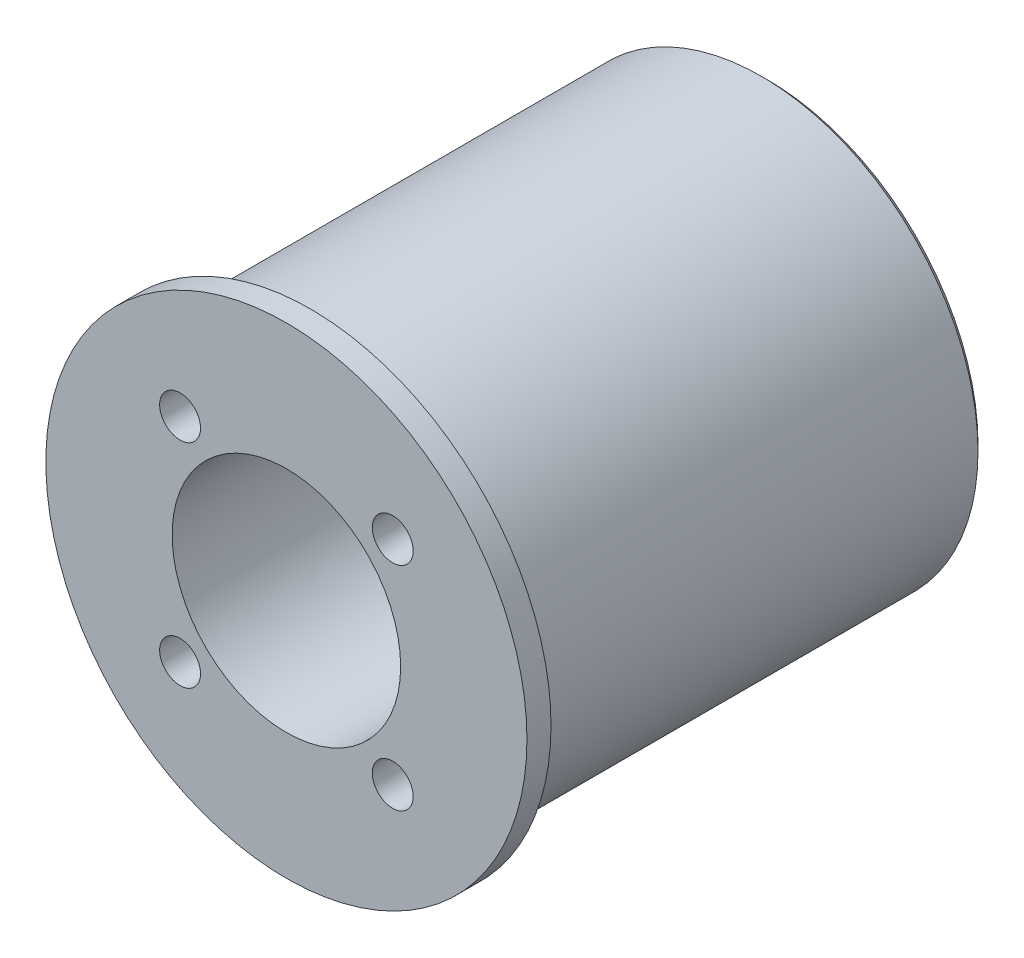
SolidWorks part; units mm, degrees
material "AISI 1020 Acier laminé à froid"
ref_plane "Plan de face" through (0, 0, 0) normal (0, 0, 1) x (1, 0, 0)
ref_plane "Plan de dessus" through (0, 0, 0) normal (0, 1, 0) x (1, 0, 0)
ref_plane "Plan de droite" through (0, 0, 0) normal (1, 0, 0) x (0, 0, -1)
sketch "Esquisse1" plane through (0, 0, 0) normal (0, 0, 1) x (1, 0, 0)
  circle A0 centre (0, 0) radius 18
  dimension "D1" = 36
extrude "Boss.-Extru.1" add sketch "Esquisse1" along normal blind 40
sketch "Sketch1" plane through (0, 0, 40) normal (0, 0, 1) x (1, 0, 0)
  circle A0 centre (0, 0) radius 20
  dimension "D1" = 40
extrude "Boss-Extrude1" add sketch "Sketch1" against normal blind 2
hole_wizard "CBORE for M3 Hex Socket Head Cap Screw1" positions "Esquisse2" profile "Esquisse4" counterbore size "M3" standard "ISO" end condition through all
sketch "Esquisse2" plane through (0, 0, 0) normal (0, 0, -1) x (-1, 0, 0)
  line L8 (8.8388, -8.8388) -> (-8.8388, -8.8388) construction
  line L9 (8.8388, -8.8388) -> (8.8388, 8.8388) construction
  line L10 (8.8388, 8.8388) -> (-8.8388, 8.8388) construction
  line L11 (-8.8388, -8.8388) -> (-8.8388, 8.8388) construction
  line L12 (8.8388, -8.8388) -> (-8.8388, 8.8388) construction
  line L13 (8.8388, 8.8388) -> (-8.8388, -8.8388) construction
  point P0 (-8.8388, -8.8388)
  point P2 (-8.8388, 8.8388)
  point P4 (8.8388, -8.8388)
  point P6 (8.8388, 8.8388)
  point P32 (0, 0)
  dimension "D1" = 25
sketch "Esquisse4" plane through (8.8388, -8.8388, 0) normal (1, 0, 0) x (0, 1, 0)
  line L0 (0, 0) -> (0, 40)
  line L1 (0, 40) -> (1.7, 40)
  line L3 (1.7, 40) -> (1.7, 3.4)
  line L4 (1.7, 3.4) -> (3.25, 3.4)
  line L5 (3.25, 3.4) -> (3.25, 0)
  line L7 (3.25, 0) -> (0, 0)
  line L11 (0, -6.35) -> (0, 107.95) construction
  dimension "Diamètre du perçage jusqu'au prochain" = 3.4
  dimension "Profondeur du perçage jusqu'au prochain" = 40
  dimension "Diamètre du chambrage" = 6.5
  dimension "Profondeur du chambrage" = 3.4
sketch "Esquisse5" plane through (0, 0, 40) normal (0, 0, 1) x (1, 0, 0)
  circle A0 centre (0, 0) radius 9.5
  dimension "D1" = 19
extrude "Enlèv. mat.-Extru.1" cut sketch "Esquisse5" against normal offset from surface (35 mm away) 5 up to face at (5.5888, -8.8388, 0)
sketch "Esquisse6" plane through (0, 0, 0) normal (0, 0, -1) x (-1, 0, 0)
  circle A0 centre (0, 0) radius 8
  dimension "D1" = 16
extrude "Cut-Extrude2" cut sketch "Esquisse6" against normal through all
chamfer "Chamfer1" distance 0.5 angle 45 1 edges at (18, 0, 0)
